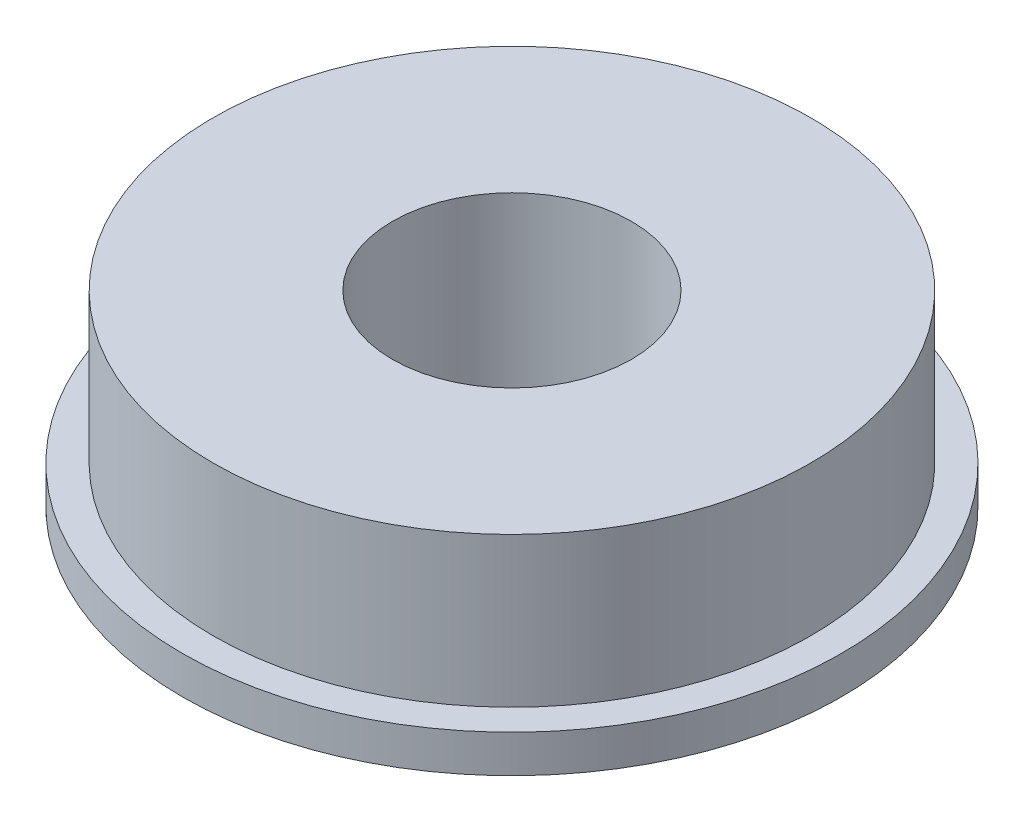
SolidWorks part; units mm, degrees
ref_plane "Front Plane" through (0, 0, 0) normal (0, 0, 1) x (1, 0, 0)
ref_plane "Top Plane" through (0, 0, 0) normal (0, 1, 0) x (1, 0, 0)
ref_plane "Right Plane" through (0, 0, 0) normal (1, 0, 0) x (0, 0, -1)
sketch "Sketch1" plane through (0, 0, 0) normal (0, 1, 0) x (1, 0, 0)
  circle A0 centre (0, 0) radius 8.75
  dimension "D1" = 17.5
extrude "Boss-Extrude1" add sketch "Sketch1" along normal blind 1
sketch "Sketch2" plane through (0, 1, 0) normal (0, 1, 0) x (1, 0, 0)
  circle A0 centre (0, 0) radius 7.9375
  dimension "D1" = 15.875
extrude "Boss-Extrude2" add sketch "Sketch2" along normal blind 3.973
sketch "Sketch3" plane through (0, 4.973, 0) normal (0, 1, 0) x (1, 0, 0)
  circle A0 centre (0, 0) radius 3.175
  dimension "D1" = 6.35
extrude "Cut-Extrude1" cut sketch "Sketch3" against normal through all
